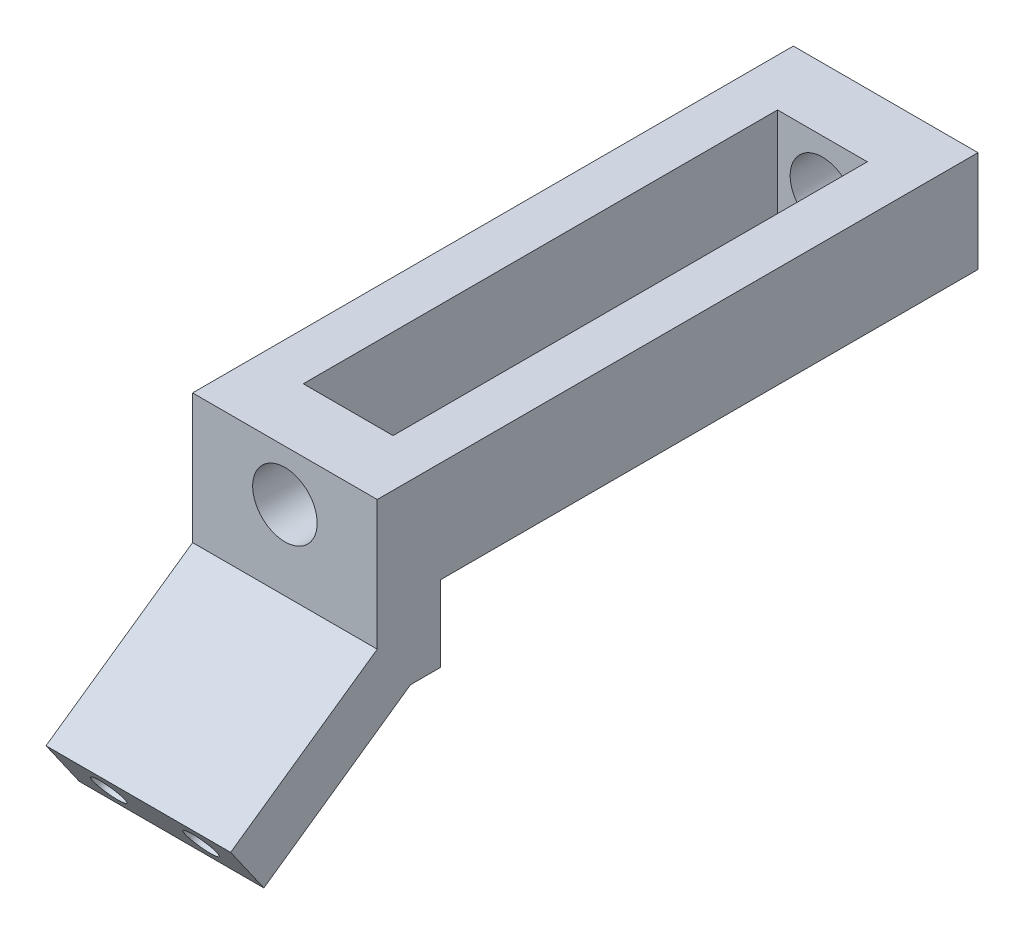
SolidWorks part; units mm, degrees
ref_plane "Front Plane" through (0, 0, 0) normal (0, 0, 1) x (1, 0, 0)
ref_plane "Top Plane" through (0, 0, 0) normal (0, 1, 0) x (1, 0, 0)
ref_plane "Right Plane" through (0, 0, 0) normal (1, 0, 0) x (0, 0, -1)
sketch "Sketch1" plane through (0, 0, 0) normal (0, 0, 1) x (1, 0, 0)
  line L0 (-5.1, 0) -> (-7.1, 0) construction
  line L1 (-7.1, 0) -> (-7.1, 8) construction
  line L2 (-7.1, 8) -> (-14.6, 8)
  line L3 (-14.6, 8) -> (-14.6, -8)
  line L4 (-14.6, -8) -> (-7.1, -8)
  line L5 (-7.1, -8) -> (-7.1, 0) construction
  line L6 (5.1, 0) -> (7.1, 0) construction
  line L7 (7.1, 8) -> (7.1, 0) construction
  line L8 (7.1, 0) -> (7.1, -8) construction
  line L9 (7.1, -8) -> (14.6, -8)
  line L10 (14.6, -8) -> (14.6, 8)
  line L11 (14.6, 8) -> (7.1, 8)
  line L12 (-7.1, -8) -> (7.1, -8)
  line L13 (-7.1, 8) -> (7.1, 8)
  circle A0 centre (0, 0) radius 5.1
  dimension "D1" = 10.2
  dimension "D6" = 8
  dimension "D2" = 2
  dimension "D3" = 7.5
  dimension "D4" = 2
  dimension "D5" = 7.5
extrude "Boss-Extrude1" add sketch "Sketch1" along normal blind 10
sketch "Sketch2" plane through (0, 0, 10) normal (0, 0, 1) x (1, 0, 0)
  line L0 (-14.6, -8) -> (14.6, -8) construction
  line L1 (-14.6, 8) -> (-7.1, 8)
  line L2 (-14.6, 8) -> (-14.6, -8)
  line L3 (-14.6, -8) -> (-7.1, -8)
  line L4 (-7.1, 8) -> (-7.1, -8)
  line L6 (14.6, 8) -> (7.1, 8)
  line L7 (14.6, 8) -> (14.6, -8)
  line L8 (14.6, -8) -> (7.1, -8)
  line L9 (7.1, 8) -> (7.1, -8)
  dimension "D1" = 7.5
  dimension "D2" = 7.5
extrude "Boss-Extrude2" add sketch "Sketch2" along normal blind 85
sketch "Sketch3" plane through (0, 0, 95) normal (0, 0, 1) x (1, 0, 0)
  line L0 (-14.6, 8) -> (14.6, 8)
  line L1 (14.6, 8) -> (14.6, -8)
  line L2 (14.6, -8) -> (-14.6, -8)
  line L3 (-14.6, -8) -> (-14.6, 8)
  circle A0 centre (0, 0) radius 5.1
  circle A1 centre (0, 0) radius 5.1 construction
extrude "Boss-Extrude3" add sketch "Sketch3" against normal blind 10
sketch "Sketch4" plane through (0, 0, 95) normal (0, 0, 1) x (1, 0, 0)
  line L0 (-14.6, -12.5) -> (14.6, -12.5) construction
  line L1 (-14.6, -8) -> (14.6, -8)
  line L2 (-14.6, -8) -> (-14.6, -20)
  line L3 (-14.6, -20) -> (14.6, -20)
  line L4 (14.6, -8) -> (14.6, -20)
  point P7 (14.2796, -12.5)
  point P9 (14.6, -8)
  dimension "D1" = 12.5
  dimension "D2" = 7.5
extrude "Boss-Extrude4" add sketch "Sketch4" against normal blind 10
sketch "Sketch5" plane through (14.6, 0, 0) normal (1, 0, 0) x (0, 0, -1)
  line L0 (-95, -12.5) -> (-85, -12.5) construction
  line L1 (-95, -20) -> (-95, 8) construction
  line L2 (-95, -12.5) -> (-89.7484, -20)
  line L3 (-85, -20) -> (-95, -20) construction
  line L4 (-95, -12.5) -> (-95, -20)
  line L5 (-95, -20) -> (-89.7484, -20)
  line L6 (-85, -20) -> (-85, -8) construction
  line L7 (0, 0) -> (-95, 0) construction
  dimension "D1" = 35
  dimension "D2" = 12.5
extrude "Cut-Extrude1" cut sketch "Sketch5" against normal up to next contours L5 L2 L4
sketch "Sketch6" plane through (0, -48.7478, 69.619) normal (0, -0.5736, 0.8192) x (1, 0, 0)
  line L1 (-14.6, 44.2504) -> (14.6, 44.2504)
  line L2 (-14.6, 44.2504) -> (-14.6, 35.0946)
  line L3 (-14.6, 35.0946) -> (14.6, 35.0946)
  line L4 (14.6, 44.2504) -> (14.6, 35.0946)
extrude "Boss-Extrude5" add sketch "Sketch6" along normal blind 28.3
sketch "Sketch7" plane through (0, -64.98, 92.801) normal (0, -0.5736, 0.8192) x (1, 0, 0)
  line L0 (0, 39.6725) -> (14.6, 39.6725) construction
  line L1 (-14.6, 44.2504) -> (-14.6, 35.0946) construction
  line L3 (0, 44.2504) -> (0, 35.0946) construction
  line L4 (14.6, 44.2504) -> (-14.6, 44.2504) construction
  line L5 (-14.6, 35.0946) -> (14.6, 35.0946) construction
  line L6 (-14.6, 39.6725) -> (0, 39.6725) construction
  line L7 (14.6, 35.0946) -> (14.6, 44.2504) construction
  circle A0 centre (-7.3, 39.6725) radius 2.5
  circle A1 centre (7.3, 39.6725) radius 2.5
  point P1 (7.3, 68.3513)
  dimension "D1" = 5
  dimension "D2" = 5
extrude "Cut-Extrude2" cut sketch "Sketch7" against normal blind 20
